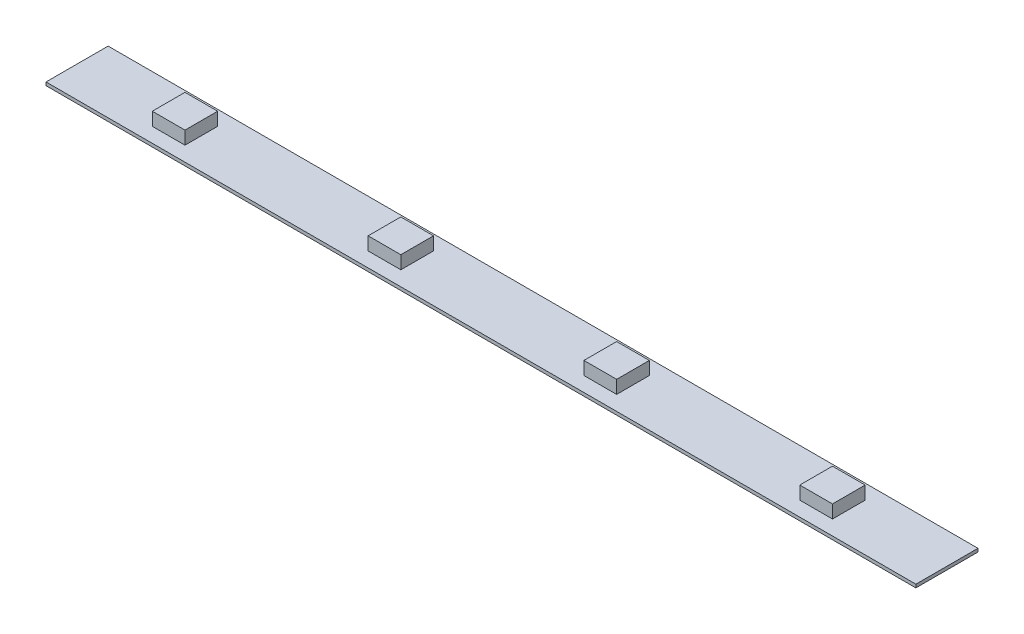
SolidWorks part; units mm, degrees
ref_plane "Plan de face" through (0, 0, 0) normal (0, 0, 1) x (1, 0, 0)
ref_plane "Plan de dessus" through (0, 0, 0) normal (0, 1, 0) x (1, 0, 0)
ref_plane "Plan de droite" through (0, 0, 0) normal (1, 0, 0) x (0, 0, -1)
sketch "Esquisse1" plane through (0, 0, 0) normal (0, 1, 0) x (1, 0, 0)
  line L1 (0, 0) -> (133, 0)
  line L2 (0, 0) -> (0, 9.5)
  line L3 (0, 9.5) -> (133, 9.5)
  line L4 (133, 0) -> (133, 9.5)
  dimension "D1" = 133
  dimension "D2" = 9.5
extrude "Boss.-Extru.1" add sketch "Esquisse1" along normal blind 0.5
sketch "Esquisse2" plane through (0, 0.5, 0) normal (0, 1, 0) x (1, 0, 0)
  line L0 (0, 9.5) -> (0, 0) construction
  line L1 (14, 7.25) -> (19, 7.25)
  line L2 (14, 7.25) -> (14, 2.25)
  line L3 (14, 2.25) -> (19, 2.25)
  line L4 (19, 7.25) -> (19, 2.25)
  line L5 (0, 9.5) -> (0, 0) construction
  line L6 (47, 7.25) -> (52, 7.25)
  line L7 (47, 7.25) -> (47, 2.25)
  line L8 (47, 2.25) -> (52, 2.25)
  line L9 (52, 7.25) -> (52, 2.25)
  line L10 (80, 7.25) -> (85, 7.25)
  line L11 (80, 7.25) -> (80, 2.25)
  line L12 (80, 2.25) -> (85, 2.25)
  line L13 (85, 7.25) -> (85, 2.25)
  line L14 (113, 7.25) -> (118, 7.25)
  line L15 (113, 7.25) -> (113, 2.25)
  line L16 (113, 2.25) -> (118, 2.25)
  line L17 (118, 7.25) -> (118, 2.25)
  point P6 (0, 4.75)
  point P11 (19, 4.75)
  point P12 (47, 4.75)
  dimension "D1" = 5
  dimension "D2" = 5
  dimension "D3" = 14
  dimension "D5" = 28
  dimension "D4" = 4
extrude "Boss.-Extru.2" add sketch "Esquisse2" along normal blind 2
